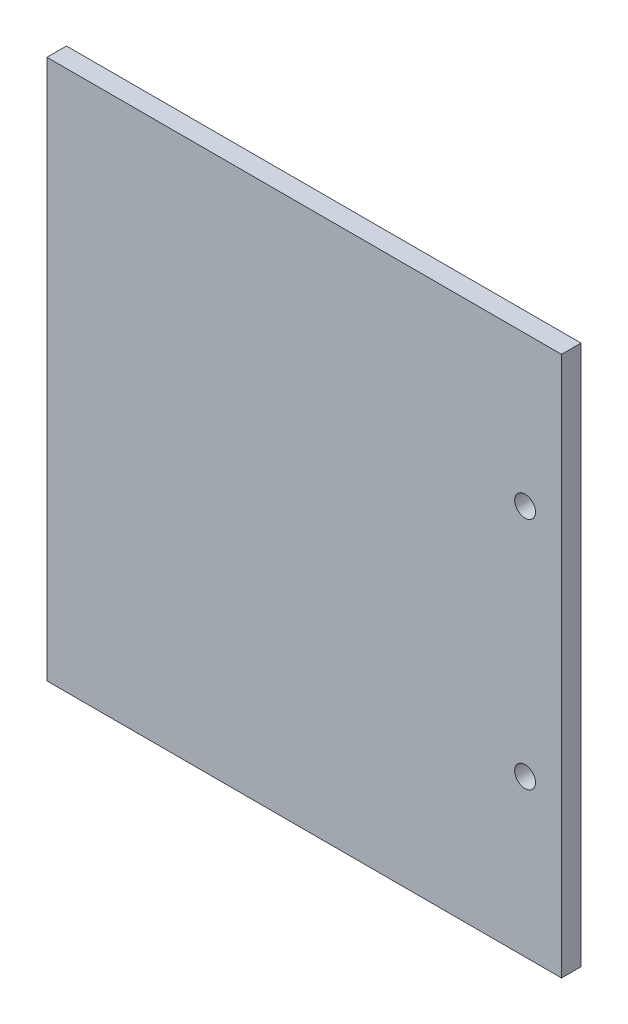
SolidWorks part; units mm, degrees
ref_plane "Front Plane" through (0, 0, 0) normal (0, 0, 1) x (1, 0, 0)
ref_plane "Top Plane" through (0, 0, 0) normal (0, 1, 0) x (1, 0, 0)
ref_plane "Right Plane" through (0, 0, 0) normal (1, 0, 0) x (0, 0, -1)
sketch "Sketch1" plane through (0, 0, 0) normal (0, 0, 1) x (1, 0, 0)
  line L0 (133.35, 0) -> (133.35, 131.7625) construction
  line L1 (16.698, 0) -> (142.24, 0)
  line L2 (16.698, 0) -> (16.698, 131.7625)
  line L3 (16.698, 131.7625) -> (142.24, 131.7625)
  line L4 (142.24, 0) -> (142.24, 131.7625)
  circle A0 centre (133.35, 38.1) radius 2.54
  circle A1 centre (133.35, 95.25) radius 2.54
extrude "Boss-Extrude1" add sketch "Sketch1" along normal blind 4.7625
